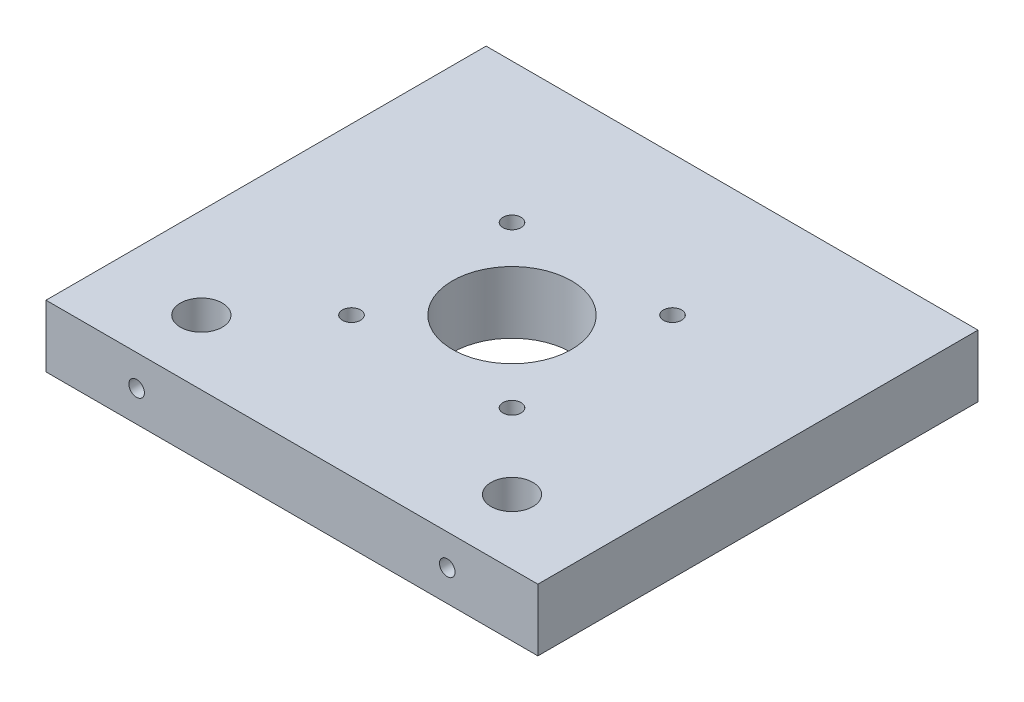
SolidWorks part; units mm, degrees
ref_plane "Front Plane" through (0, 0, 0) normal (0, 0, 1) x (1, 0, 0)
ref_plane "Top Plane" through (0, 0, 0) normal (0, 1, 0) x (1, 0, 0)
ref_plane "Right Plane" through (0, 0, 0) normal (1, 0, 0) x (0, 0, -1)
sketch "Sketch1" plane through (0, 0, 0) normal (0, 0, 1) x (1, 0, 0)
  line L1 (-47.5, 6) -> (47.5, 6)
  line L2 (-47.5, 6) -> (-47.5, -6)
  line L3 (-47.5, -6) -> (47.5, -6)
  line L4 (47.5, 6) -> (47.5, -6)
  line L5 (-47.5, 6) -> (47.5, -6) construction
  line L6 (-47.5, -6) -> (47.5, 6) construction
  point P0 (0, 0)
  dimension "D1" = 12
  dimension "D2" = 95
extrude "Boss-Extrude1" add sketch "Sketch1" along normal blind 85
sketch "Sketch2" plane through (0, -6, 0) normal (0, -1, 0) x (1, 0, 0)
  line L0 (-47.5, 85) -> (47.5, 85) construction
  line L1 (-47.5, 85) -> (-47.5, 0) construction
  line L2 (47.5, 85) -> (47.5, 0) construction
  line L3 (47.5, 85) -> (-47.5, 85) construction
  circle A0 centre (-30, 72.5) radius 4.05
  circle A1 centre (30, 72.5) radius 4.05
  circle A2 centre (0, 42.5) radius 11.5
  point P13 (0, 85)
  dimension "D1" = 8.1
  dimension "D2" = 8.1
  dimension "D3" = 23
  dimension "D4" = 12.5
  dimension "D5" = 17.5
  dimension "12.5" = 12.5
  dimension "D6" = 42.5
  dimension "D7" = 17.5
  dimension "D8" = 47.5
extrude "Cut-Extrude1" cut sketch "Sketch2" against normal through all
sketch "Sketch4" plane through (0, 0, 85) normal (0, 0, 1) x (1, 0, 0)
  line L0 (47.5, -6) -> (47.5, 6) construction
  line L1 (-47.5, 6) -> (-47.5, -6) construction
  circle A0 centre (30, 0) radius 1.5
  circle A1 centre (-30, 0) radius 1.5
  point P4 (47.5, 0)
  point P7 (-47.5, 0)
  dimension "D1" = 3
  dimension "D2" = 3
  dimension "D3" = 17.5
  dimension "D4" = 17.5
extrude "Cut-Extrude3" cut sketch "Sketch4" against normal up to next
sketch "Sketch6" plane through (0, -6, 0) normal (0, -1, 0) x (1, 0, 0)
  line L0 (-47.5, 85) -> (47.5, 85) construction
  line L1 (-47.5, 85) -> (-47.5, 0) construction
  line L2 (47.5, 85) -> (47.5, 0) construction
  circle A0 centre (-15.5, 58) radius 1.75
  circle A1 centre (-15.5, 27) radius 1.75
  circle A2 centre (15.5, 58) radius 1.75
  circle A3 centre (15.5, 27) radius 1.75
  dimension "D8" = 3.5
  dimension "D9" = 3.5
  dimension "D10" = 3.5
  dimension "D11" = 3.5
  dimension "D1" = 27
  dimension "D2" = 27
  dimension "D3" = 32
  dimension "D4" = 32
  dimension "D5" = 31
  dimension "D6" = 31
  dimension "D7" = 31
  dimension "D12" = 32
extrude "Cut-Extrude4" cut sketch "Sketch6" against normal through all
